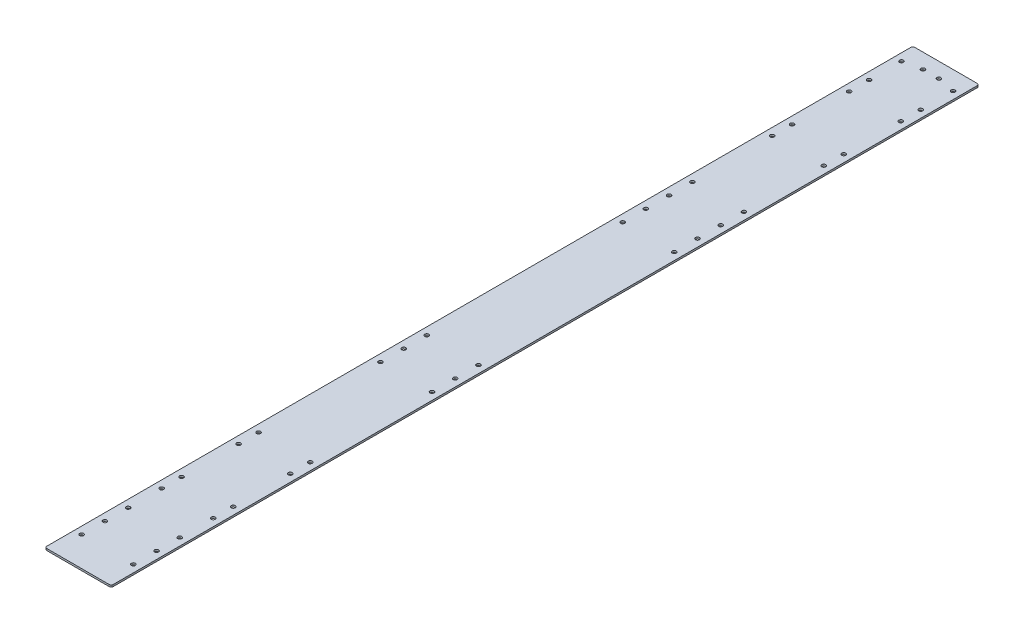
SolidWorks part; units mm, degrees
ref_plane "Front Plane" through (0, 0, 0) normal (0, 0, 1) x (1, 0, 0)
ref_plane "Top Plane" through (0, 0, 0) normal (0, 1, 0) x (1, 0, 0)
ref_plane "Right Plane" through (0, 0, 0) normal (1, 0, 0) x (0, 0, -1)
sketch "Sketch1" plane through (0, 0, 0) normal (0, 1, 0) x (1, 0, 0)
  line L1 (3, 0) -> (97, 0)
  line L2 (0, 3) -> (0, 1305)
  line L3 (3, 1308) -> (97, 1308)
  line L4 (100, 3) -> (100, 1305)
  arc A0 (97, 0) -> (100, 3) centre (97, 3) ccw
  arc A1 (97, 1308) -> (100, 1305) centre (97, 1305) cw
  arc A2 (3, 0) -> (0, 3) centre (3, 3) cw
  arc A3 (0, 1305) -> (3, 1308) centre (3, 1305) cw
  point P9 (100, 1308)
  point P12 (0, 0)
  point P15 (0, 1308)
  dimension "D3" = 3
  dimension "D1" = 100
  dimension "D2" = 1308
extrude "Boss-Extrude1" add sketch "Sketch1" along normal blind 2.8
sketch "Sketch2" plane through (0, 2.8, 0) normal (0, 1, 0) x (1, 0, 0)
  line L0 (50, 1308) -> (50, 0) construction
  line L1 (97, 1308) -> (3, 1308) construction
  line L2 (3, 0) -> (97, 0) construction
  line L3 (100, 3) -> (100, 1305) construction
  line L4 (88.9, 1279.78) -> (88.9, 929.61) construction
  line L5 (88.9, 929.61) -> (88.9, 529.56) construction
  line L6 (88.9, 529.56) -> (88.9, 79.44) construction
  circle A0 centre (88.9, 1279.78) radius 3
  circle A1 centre (88.9, 929.61) radius 3
  circle A2 centre (88.9, 529.56) radius 3
  circle A3 centre (88.9, 79.44) radius 3
  circle A4 centre (11.1, 79.44) radius 3
  circle A5 centre (11.1, 529.56) radius 3
  circle A6 centre (11.1, 929.61) radius 3
  circle A7 centre (11.1, 1279.78) radius 3
  dimension "D1" = 6
  dimension "D2" = 11.1
  dimension "D3" = 28.22
  dimension "D5" = 350.17
  dimension "D7" = 400.05
  dimension "D9" = 450.12
  dimension "D4" = 2
  dimension "D6" = 2
  dimension "D8" = 2
extrude "Cut-Extrude1" cut sketch "Sketch2" against normal up to next
sketch "Sketch3" plane through (0, 2.8, 0) normal (0, 1, 0) x (1, 0, 0)
  line L0 (100, 3) -> (100, 1305) construction
  line L1 (97, 1308) -> (3, 1308) construction
  line L2 (50, 1308) -> (50, 1158) construction
  circle A0 centre (88.9, 1201) radius 3
  circle A1 centre (88.9, 1115) radius 3
  circle A2 centre (11.1, 1115) radius 3
  circle A3 centre (11.1, 1201) radius 3
  circle A4 centre (88.9, 281) radius 3
  circle A5 centre (88.9, 195) radius 3
  circle A6 centre (11.1, 195) radius 3
  circle A7 centre (11.1, 281) radius 3
  dimension "D1" = 6
  dimension "D2" = 86
  dimension "D3" = 107
  dimension "D5" = 11.1
  dimension "D6" = 834
  dimension "D4" = 2
extrude "Cut-Extrude2" cut sketch "Sketch3" against normal up to next
sketch "Sketch4" plane through (0, 2.8, 0) normal (0, 1, 0) x (1, 0, 0)
  line L0 (50, 1308) -> (50, 1218.2999) construction
  line L1 (97, 1308) -> (3, 1308) construction
  line L2 (100, 3) -> (100, 1305) construction
  circle A0 centre (88.9, 1231) radius 3
  circle A1 centre (88.9, 1201) radius 3 construction
  circle A2 centre (88.9, 1085) radius 3
  circle A3 centre (88.9, 1115) radius 3 construction
  circle A4 centre (88.9, 964.61) radius 3
  circle A5 centre (88.9, 894.61) radius 3
  circle A6 centre (88.9, 929.61) radius 3 construction
  circle A7 centre (88.9, 564.56) radius 3
  circle A8 centre (88.9, 494.56) radius 3
  circle A9 centre (88.9, 529.56) radius 3 construction
  circle A10 centre (88.9, 114.44) radius 3
  circle A11 centre (88.9, 44.44) radius 3
  circle A12 centre (88.9, 79.44) radius 3 construction
  circle A13 centre (88.9, 311) radius 3
  circle A14 centre (88.9, 165) radius 3
  circle A15 centre (88.9, 281) radius 3 construction
  circle A16 centre (88.9, 195) radius 3 construction
  circle A17 centre (11.1, 165) radius 3
  circle A18 centre (11.1, 311) radius 3
  circle A19 centre (11.1, 44.44) radius 3
  circle A20 centre (11.1, 114.44) radius 3
  circle A21 centre (11.1, 494.56) radius 3
  circle A22 centre (11.1, 564.56) radius 3
  circle A23 centre (11.1, 894.61) radius 3
  circle A24 centre (11.1, 964.61) radius 3
  circle A25 centre (11.1, 1085) radius 3
  circle A26 centre (11.1, 1231) radius 3
  circle A27 centre (88.9, 859.61) radius 3
  circle A28 centre (11.1, 859.61) radius 3
  dimension "D1" = 6
  dimension "D2" = 11.1
  dimension "D3" = 30
  dimension "D4" = 30
  dimension "D5" = 35
  dimension "D6" = 35
  dimension "D7" = 35
  dimension "D8" = 35
  dimension "D9" = 35
  dimension "D10" = 30
  dimension "D11" = 35
  dimension "D12" = 30
  dimension "D13" = 35
extrude "Cut-Extrude3" cut sketch "Sketch4" against normal up to next
sketch "Sketch5" plane through (0, 2.8, 0) normal (0, 1, 0) x (1, 0, 0)
  line L0 (50, 1308) -> (50, 1275.2854) construction
  line L1 (97, 1308) -> (3, 1308) construction
  circle A0 centre (37.99, 1285.31) radius 3
  circle A1 centre (62.01, 1285.31) radius 3
  dimension "D1" = 6
  dimension "D2" = 22.69
  dimension "D3" = 12.01
extrude "Cut-Extrude4" cut sketch "Sketch5" against normal up to next
